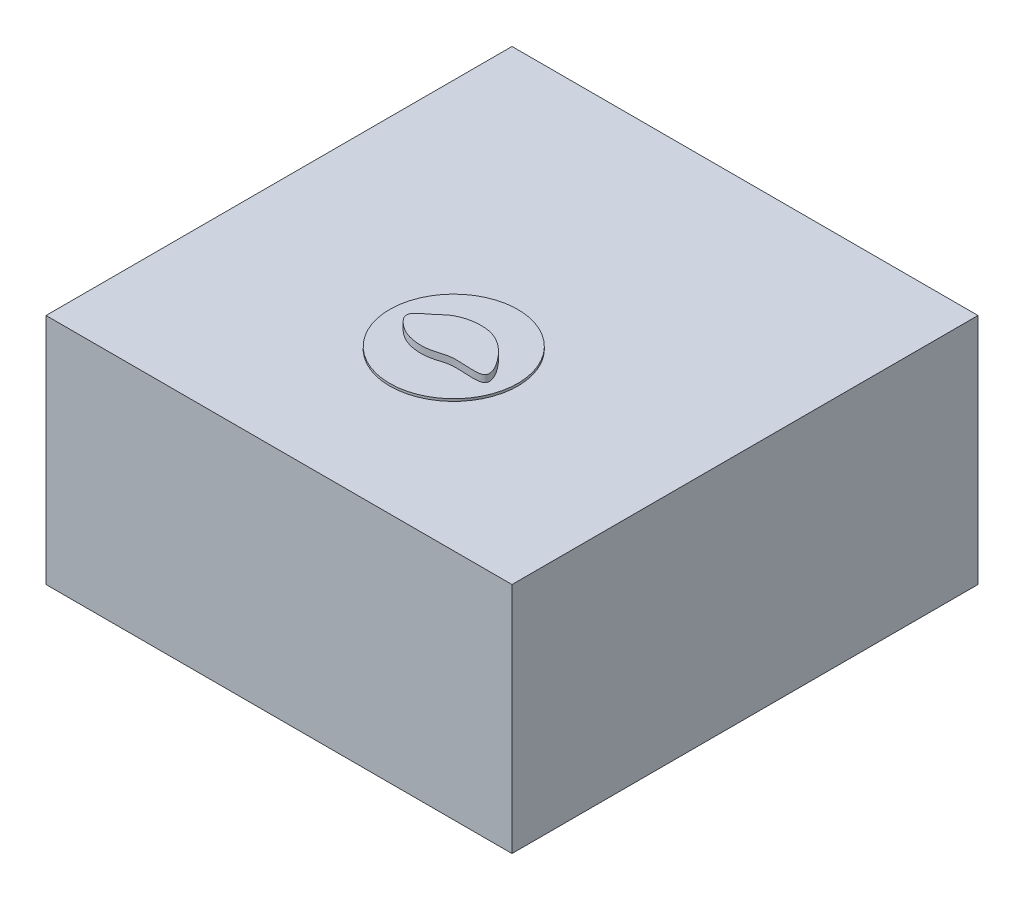
SolidWorks part; units mm, degrees
ref_plane "Front Plane" through (0, 0, 0) normal (0, 0, 1) x (1, 0, 0)
ref_plane "Top Plane" through (0, 0, 0) normal (0, 1, 0) x (1, 0, 0)
ref_plane "Right Plane" through (0, 0, 0) normal (1, 0, 0) x (0, 0, -1)
sketch "Sketch1" plane through (0, 0, 0) normal (0, 0, 1) x (1, 0, 0)
  line L1 (-10, -5) -> (10, -5)
  line L2 (-10, -5) -> (-10, 5)
  line L3 (-10, 5) -> (10, 5)
  line L4 (10, -5) -> (10, 5)
  line L5 (0, 5) -> (0, -5) construction
  line L6 (-10, 0) -> (10, 0) construction
  point P0 (0, 0)
  dimension "D1" = 20
  dimension "D2" = 10
extrude "Boss-Extrude1" add sketch "Sketch1" along normal blind 20
sketch "Sketch2" plane through (0, 0, 20) normal (0, 0, 1) x (1, 0, 0)
  line L0 (-10, -5) -> (10, -5) construction
  line L1 (0, 0) -> (0, -5) construction
  line L3 (10, 5) -> (-10, 5) construction
  circle A0 centre (-7.5, 4) radius 0.5
  circle A1 centre (7.5, 4) radius 0.5
  dimension "D1" = 1
  dimension "D2" = 7.5
  dimension "D3" = 1
ref_plane "Plane1" through (7.5, 0, 0) normal (1, 0, 0) x (0, 0, -1)
sketch "Sketch3" plane through (7.5, 0, 0) normal (1, 0, 0) x (0, 0, -1)
  line L3 (-20, 4) -> (-5, 4)
  line L4 (-20, 4.5) -> (-20, 3.5) construction
  line L5 (-20, 5) -> (0, 5) construction
  arc A0 (-5, 4) -> (-4, 5) centre (-5, 5) ccw
  dimension "D1" = 1
  dimension "D2" = 15
sweep "ag/agcl electrodes" add profiles "Sketch2" path "Sketch3"
sketch "Sketch5" plane through (0, 5, 0) normal (0, 1, 0) x (1, 0, 0)
  line L0 (0, -12.5) -> (2.75, -12.5) construction
  line L2 (0, -12.5) -> (0, -9.75) construction
  line L3 (-10, -20) -> (-10, 0) construction
  line L5 (10, -20) -> (-10, -20) construction
  circle A0 centre (0, -12.5) radius 2.75
  dimension "D1" = 5.5
  dimension "D2" = 10
  dimension "D3" = 7.5
extrude "Boss-Extrude4" add sketch "Sketch5" along normal blind 0.1 separate body
sketch "Sketch8" plane through (0, 5.1, 0) normal (0, -1, 0) x (-1, 0, 0)
  line L0 (0, -12.5) -> (2.75, -12.5) construction
  line L2 (0, -12.5) -> (0, -9.75) construction
  circle A1 centre (0, -12.5) radius 0.005
  circle A2 centre (0.5, -12.5) radius 0.005
  circle A3 centre (0.5, -12) radius 0.005
  circle A4 centre (0, -12) radius 0.005
  circle A5 centre (0.5, -13) radius 0.005
  circle A6 centre (0, -13) radius 0.005
  circle A7 centre (-0.5, -13) radius 0.005
  circle A8 centre (-0.5, -12) radius 0.005
  circle A9 centre (-0.5, -12.5) radius 0.005
  circle A10 centre (0, -12.5) radius 2.75 construction
  dimension "D1" = 0.5
  dimension "D2" = 0.01
  dimension "D5" = 0.5
  dimension "D3" = 2
  dimension "D4" = 2
extrude "Boss-Extrude5" add sketch "Sketch8" along normal blind 0.1 separate body
sketch "Sketch4" plane through (0, 5.1, 0) normal (0, 1, 0) x (1, 0, 0)
  line L0 (0, -11.4373) -> (0, -13.4201) construction
  line L1 (-2.0803, -12.5) -> (1.6023, -12.5) construction
  spline S0 degree 3 poles (-2.0861, -12.5392) (-1.3776, -12.1296) (-0.8241, -11.549) (0.2513, -11.3226) (1.3726, -11.7466) (2.6529, -13.5718) (0.7805, -13.1045) (-0.1221, -13.5063) (-0.9948, -13.461) (-1.5864, -13.1169) (-2.0861, -12.5392) (-1.3776, -12.1296) (-0.8241, -11.549) knots -0.204834 -0.133435 -0.089031 0 0.049563 0.182818 0.303261 0.461561 0.613381 0.684438 0.795166 0.866565 0.910969 1 1.049563 1.182818 1.303261 only from (-1.3298, -12.0471) to (-1.3298, -12.0471)
extrude "slice" add sketch "Sketch4" along normal blind 0.3 separate body
